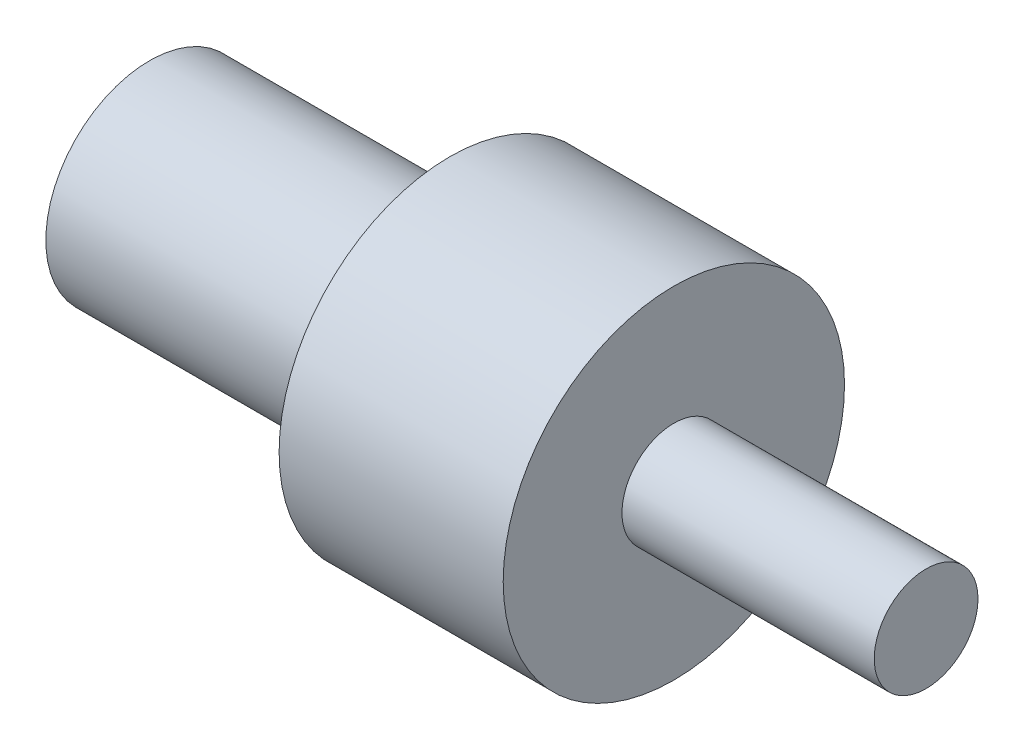
SolidWorks part; units mm, degrees
ref_plane "Přední rovina" through (0, 0, 0) normal (0, 0, 1) x (1, 0, 0)
ref_plane "Horní rovina" through (0, 0, 0) normal (0, 1, 0) x (1, 0, 0)
ref_plane "Pravá rovina" through (0, 0, 0) normal (1, 0, 0) x (0, 0, -1)
sketch "Skica1" plane through (0, 0, 0) normal (0, 0, 1) x (1, 0, 0)
  line L0 (292.4973, 0) -> (-292.4973, 0) construction
  line L1 (0, 0) -> (0, 17.5457)
  line L2 (0, 17.5457) -> (50.7492, 17.5457)
  line L3 (50.7492, 17.5457) -> (50.7492, 28.8526)
  line L4 (50.7492, 28.8526) -> (88.637, 28.8526)
  line L5 (88.637, 28.8526) -> (88.637, 8.7729)
  line L6 (88.637, 8.7729) -> (131.2856, 8.7729)
  line L7 (131.2856, 8.7729) -> (131.2856, 0)
  line L8 (131.2856, 0) -> (0, 0)
  point P4 (0, 0)
revolve "Rotovat1" add sketch "Skica1" angle 360 about L8
